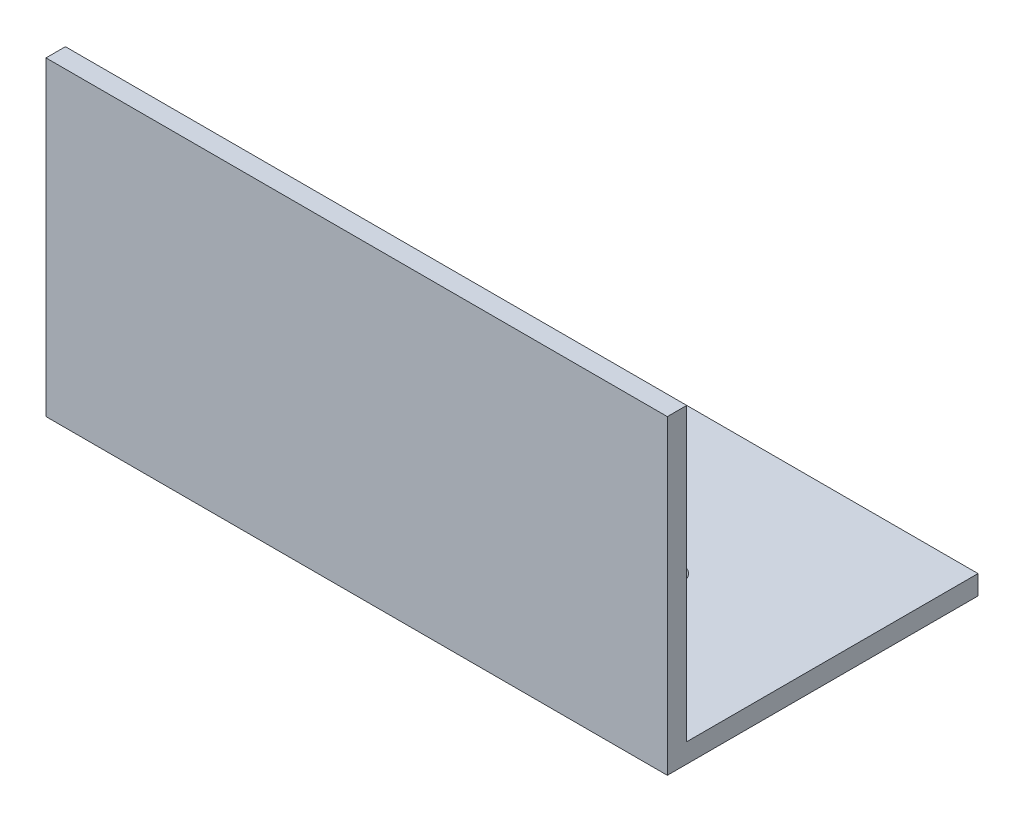
SolidWorks part; units mm, degrees
material "Alloy Steel"
ref_plane "Front Plane" through (0, 0, 0) normal (0, 0, 1) x (1, 0, 0)
ref_plane "Top Plane" through (0, 0, 0) normal (0, 1, 0) x (1, 0, 0)
ref_plane "Right Plane" through (0, 0, 0) normal (1, 0, 0) x (0, 0, -1)
sketch "Sketch1" plane through (0, 0, 0) normal (1, 0, 0) x (0, 0, -1)
  line L0 (0, 0) -> (0, 50.8)
  line L1 (0, 50.8) -> (3.175, 50.8)
  line L2 (3.175, 50.8) -> (3.175, 3.175)
  line L3 (3.175, 3.175) -> (50.8, 3.175)
  line L4 (50.8, 3.175) -> (50.8, 0)
  line L5 (50.8, 0) -> (0, 0)
  dimension "D1" = 50.8
  dimension "D2" = 3.175
extrude "Boss-Extrude1" add sketch "Sketch1" along normal blind 101.6
hole_wizard "#10 (0.1935) Diameter Hole1" positions "Sketch2" profile "Sketch3" hole size "#10" standard "ANSI Inch" end condition through all
sketch "Sketch2" plane through (0, 0, 0) normal (0, -1, 0) x (-1, 0, 0)
  line L0 (-101.6, 0) -> (-101.6, 50.8) construction
  line L1 (-101.6, 0) -> (0, 0) construction
  point P0 (-76.2, 25.4)
  point P2 (-25.4, 25.4)
  point P5 (0, 0)
  dimension "D1" = 25.4
  dimension "D2" = 50.8
  dimension "D3" = 25.4
sketch "Sketch3" plane through (76.2, 0, -25.4) normal (1, 0, 0) x (0, 0, -1)
  line L0 (0, 0) -> (0, 50.8)
  line L1 (0, 50.8) -> (2.4574, 50.8)
  line L2 (2.4574, 50.8) -> (2.4574, 0)
  line L5 (2.4574, 0) -> (0, 0)
  line L11 (0, -6.35) -> (0, 107.95) construction
  dimension "Thru Hole Dia." = 4.9149
  dimension "Thru Hole Depth" = 50.8
